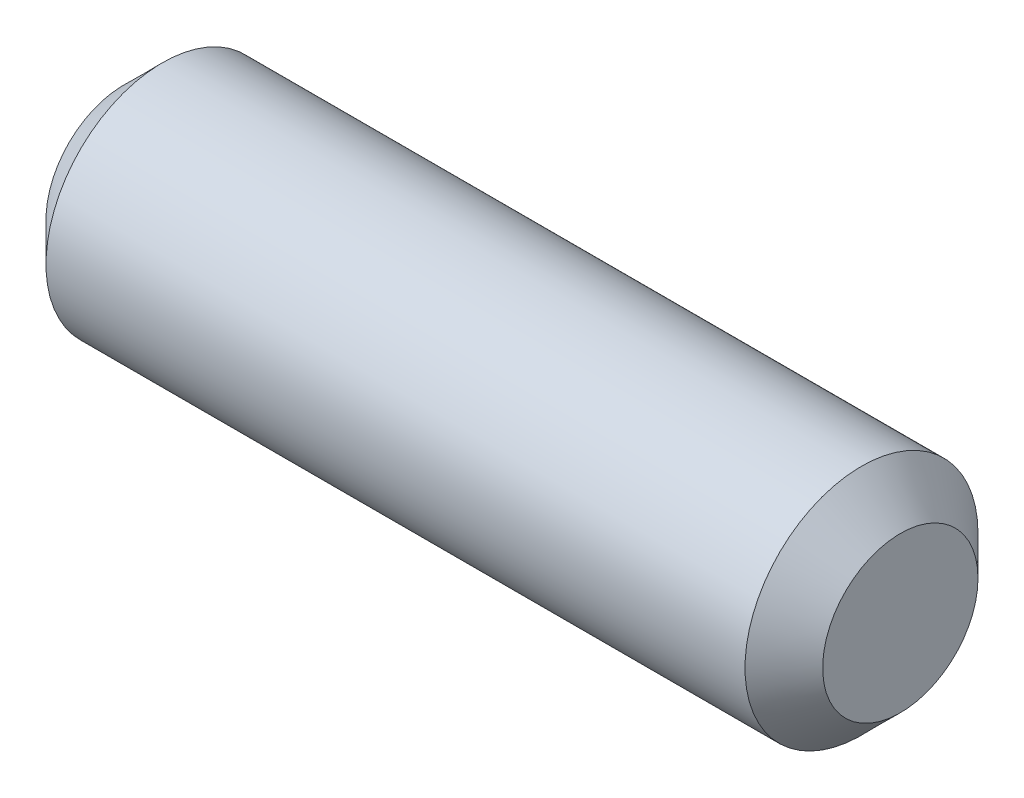
SolidWorks part; units mm, degrees
material "AISI 304"
ref_plane "Plan de face" through (0, 0, 0) normal (0, 0, 1) x (1, 0, 0)
ref_plane "Plan de dessus" through (0, 0, 0) normal (0, 1, 0) x (1, 0, 0)
ref_plane "Plan de droite" through (0, 0, 0) normal (1, 0, 0) x (0, 0, -1)
sketch "Esquisse1" plane through (0, 0, 0) normal (1, 0, 0) x (0, 0, -1)
  circle A0 centre (0, 0) radius 1.5
  dimension "D1" = 3
extrude "AXE" add sketch "Esquisse1" along normal mid plane 10
chamfer "Chanfrein1" distance 0.5 angle 45 2 edges at (-5, 0, -1.5) (5, 0, -1.5)
